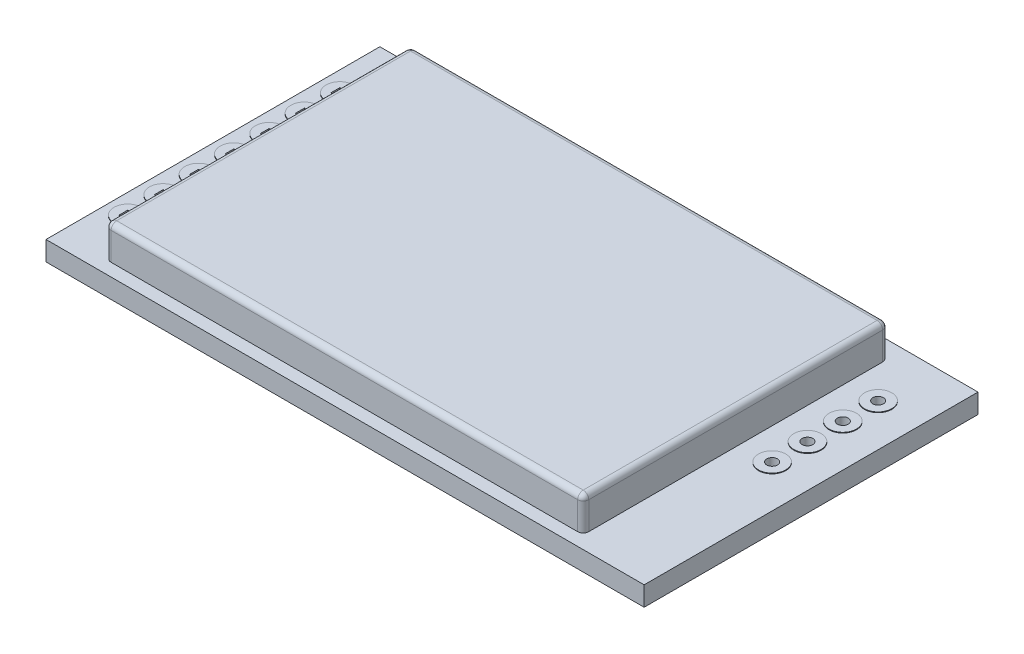
SolidWorks part; units mm, degrees
ref_plane "Alzado" through (0, 0, 0) normal (0, 0, 1) x (1, 0, 0)
ref_plane "Planta" through (0, 0, 0) normal (0, 1, 0) x (1, 0, 0)
ref_plane "Vista lateral" through (0, 0, 0) normal (1, 0, 0) x (0, 0, -1)
sketch "Croquis1" plane through (0, 0, 0) normal (0, 1, 0) x (1, 0, 0)
  line L1 (21.5, 12) -> (-21.5, 12)
  line L2 (21.5, 12) -> (21.5, -12)
  line L3 (21.5, -12) -> (-21.5, -12)
  line L4 (-21.5, 12) -> (-21.5, -12)
  line L5 (21.5, 12) -> (-21.5, -12) construction
  line L6 (21.5, -12) -> (-21.5, 12) construction
  point P0 (0, 0)
  dimension "D1" = 43
  dimension "D2" = 24
extrude "Saliente-Extruir1" add sketch "Croquis1" along normal blind 1.4
sketch "Croquis2" plane through (0, 1.4, 0) normal (0, 1, 0) x (1, 0, 0)
  line L0 (-21.5, 12) -> (-21.5, -12) construction
  line L2 (21.5, 12) -> (-21.5, 12) construction
  line L3 (21.5, -12) -> (21.5, 12) construction
  circle A0 centre (-20.02, 7.64) radius 0.9839
  circle A1 centre (-20.02, 5.1) radius 0.9839
  circle A2 centre (-20.02, 2.56) radius 0.9839
  circle A3 centre (-20.02, 0.02) radius 0.9839
  circle A4 centre (-20.02, -2.52) radius 0.9839
  circle A5 centre (-20.02, -5.06) radius 0.9839
  circle A6 centre (-20.02, -7.6) radius 0.9839
  circle A7 centre (18.5, 7.82) radius 0.985
  circle A8 centre (18.5, 5.28) radius 0.985
  circle A9 centre (18.5, 2.74) radius 0.985
  circle A10 centre (18.5, 0.2) radius 0.985
  dimension "D4" = 1.97
  dimension "D1" = 1.48
  dimension "D2" = 4.36
  dimension "D5" = 3
  dimension "D6" = 4.18
  dimension "D3" = 7
  dimension "D7" = 4
extrude "Saliente-Extruir2" add sketch "Croquis2" along normal blind 0.05
sketch "Croquis3" plane through (0, 1.45, 0) normal (0, 1, 0) x (1, 0, 0)
  line L0 (-20.34, 5.42) -> (-19.7, 5.42)
  line L1 (-20.34, 7.96) -> (-19.7, 7.96)
  line L2 (-20.34, 7.96) -> (-20.34, 7.32)
  line L3 (-20.34, 7.32) -> (-19.7, 7.32)
  line L4 (-19.7, 7.96) -> (-19.7, 7.32)
  line L5 (-20.34, 7.96) -> (-19.7, 7.32) construction
  line L6 (-20.34, 7.32) -> (-19.7, 7.96) construction
  line L7 (-20.34, 5.42) -> (-20.34, 4.78)
  line L8 (-20.34, 4.78) -> (-19.7, 4.78)
  line L9 (-19.7, 5.42) -> (-19.7, 4.78)
  line L10 (-20.34, 5.42) -> (-19.7, 4.78) construction
  line L11 (-20.34, 4.78) -> (-19.7, 5.42) construction
  line L12 (-20.34, 2.88) -> (-19.7, 2.88)
  line L13 (-20.34, 2.88) -> (-20.34, 2.24)
  line L14 (-20.34, 2.24) -> (-19.7, 2.24)
  line L15 (-19.7, 2.88) -> (-19.7, 2.24)
  line L16 (-20.34, 2.88) -> (-19.7, 2.24) construction
  line L17 (-20.34, 2.24) -> (-19.7, 2.88) construction
  line L18 (-20.34, 0.34) -> (-19.7, 0.34)
  line L19 (-20.34, 0.34) -> (-20.34, -0.3)
  line L20 (-20.34, -0.3) -> (-19.7, -0.3)
  line L21 (-19.7, 0.34) -> (-19.7, -0.3)
  line L22 (-20.34, 0.34) -> (-19.7, -0.3) construction
  line L23 (-20.34, -0.3) -> (-19.7, 0.34) construction
  line L24 (-20.34, -2.2) -> (-19.7, -2.2)
  line L25 (-20.34, -2.2) -> (-20.34, -2.84)
  line L26 (-20.34, -2.84) -> (-19.7, -2.84)
  line L27 (-19.7, -2.2) -> (-19.7, -2.84)
  line L28 (-20.34, -2.2) -> (-19.7, -2.84) construction
  line L29 (-20.34, -2.84) -> (-19.7, -2.2) construction
  line L30 (-20.34, -4.74) -> (-19.7, -4.74)
  line L31 (-20.34, -4.74) -> (-20.34, -5.38)
  line L32 (-20.34, -5.38) -> (-19.7, -5.38)
  line L33 (-19.7, -4.74) -> (-19.7, -5.38)
  line L34 (-20.34, -4.74) -> (-19.7, -5.38) construction
  line L35 (-20.34, -5.38) -> (-19.7, -4.74) construction
  line L36 (-20.34, -7.28) -> (-19.7, -7.28)
  line L37 (-20.34, -7.28) -> (-20.34, -7.92)
  line L38 (-20.34, -7.92) -> (-19.7, -7.92)
  line L39 (-19.7, -7.28) -> (-19.7, -7.92)
  line L40 (-20.34, -7.28) -> (-19.7, -7.92) construction
  line L41 (-20.34, -7.92) -> (-19.7, -7.28) construction
  point P0 (-20.02, 7.64)
  point P7 (-20.02, 5.1)
  point P12 (-20.02, 2.56)
  point P17 (-20.02, 0.02)
  point P22 (-20.02, -2.52)
  point P27 (-20.02, -5.06)
  point P32 (-20.02, -7.6)
  dimension "D1" = 0.64
  dimension "D2" = 0.64
  dimension "D3" = 7
extrude "Cortar-Extruir1" cut sketch "Croquis3" against normal blind 1.81
sketch "Croquis4" plane through (0, 1.45, 0) normal (0, 1, 0) x (1, 0, 0)
  circle A2 centre (18.5, 5.28) radius 0.385
  circle A3 centre (18.5, 7.82) radius 0.385
  circle A4 centre (18.5, 7.82) radius 0.385
  circle A5 centre (18.5, 2.74) radius 0.385
  circle A6 centre (18.5, 0.2) radius 0.385
  dimension "D1" = 0.6
  dimension "D2" = 4
extrude "Cortar-Extruir2" cut sketch "Croquis4" against normal blind 1.81
sketch "Croquis5" plane through (0, 1.4, 0) normal (0, 1, 0) x (1, 0, 0)
  line L1 (-18.1365, 10.8416) -> (16.2019, 10.8416)
  line L2 (-18.1365, 10.8416) -> (-18.1365, -11.0834)
  line L3 (-18.1365, -11.0834) -> (16.2019, -11.0834)
  line L4 (16.2019, 10.8416) -> (16.2019, -11.0834)
extrude "Saliente-Extruir3" add sketch "Croquis5" along normal blind 2.39
fillet "Redondeo1" radius 0.4 8 edges at (16.2019, 2.595, -10.8416) (16.2019, 3.79, 0.1209) (16.2019, 2.595, 11.0834) (-0.9673, 3.79, 11.0834) (-18.1365, 2.595, 11.0834) (-18.1365, 3.79, 0.1209) (-0.9673, 3.79, -10.8416) (-18.1365, 2.595, -10.8416)
